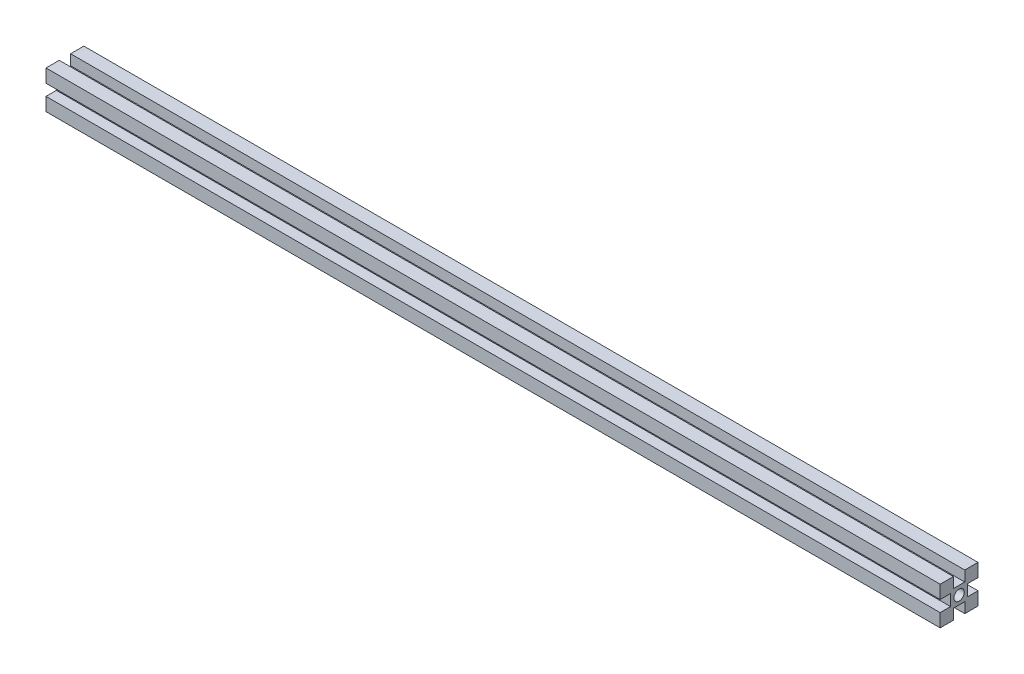
SolidWorks part; units mm, degrees
ref_plane "Plan de face" through (0, 0, 0) normal (0, 0, 1) x (1, 0, 0)
ref_plane "Plan de dessus" through (0, 0, 0) normal (0, 1, 0) x (1, 0, 0)
ref_plane "Plan de droite" through (0, 0, 0) normal (1, 0, 0) x (0, 0, -1)
ref_plane "Plan4" through (0, 0, 0) normal (-1, 0, 0) x (0, -1, 0)
sketch "Esquisse1" plane through (0, 0, 0) normal (-1, 0, 0) x (0, -1, 0)
  line L0 (-3, -10) -> (-3, -4.5)
  line L1 (-3, -4.5) -> (3, -4.5)
  line L2 (3, -4.5) -> (3, -10)
  line L3 (3, -10) -> (10, -10)
  line L4 (10, -10) -> (10, -3)
  line L5 (10, -3) -> (4.5, -3)
  line L6 (4.5, -3) -> (4.5, 3)
  line L7 (4.5, 3) -> (10, 3)
  line L8 (10, 3) -> (10, 10)
  line L9 (10, 10) -> (3, 10)
  line L10 (3, 10) -> (3, 4.5)
  line L11 (3, 4.5) -> (-3, 4.5)
  line L12 (-3, 4.5) -> (-3, 10)
  line L13 (-3, 10) -> (-10, 10)
  line L14 (-10, 10) -> (-10, 3)
  line L15 (-10, 3) -> (-4.5, 3)
  line L16 (-4.5, 3) -> (-4.5, -3)
  line L17 (-4.5, -3) -> (-10, -3)
  line L18 (-10, -3) -> (-10, -10)
  line L19 (-10, -10) -> (-3, -10)
  circle A0 centre (0, 0) radius 2.75
extrude "Boss.-Extru.1" add sketch "Esquisse1" against normal blind 472.5
